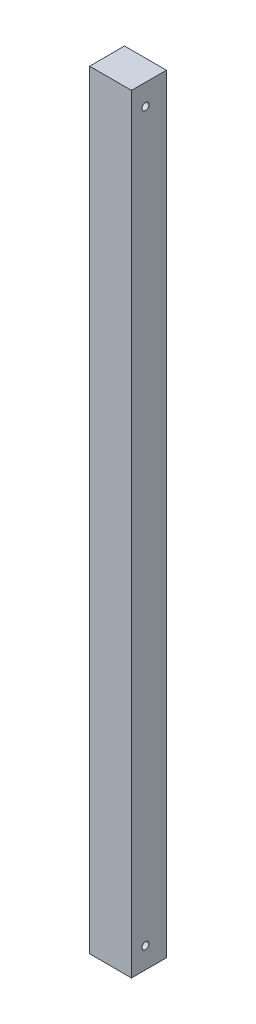
SolidWorks part; units mm, degrees
ref_plane "Front Plane" through (0, 0, 0) normal (0, 0, 1) x (1, 0, 0)
ref_plane "Top Plane" through (0, 0, 0) normal (0, 1, 0) x (1, 0, 0)
ref_plane "Right Plane" through (0, 0, 0) normal (1, 0, 0) x (0, 0, -1)
sketch "Sketch1" plane through (0, 0, 0) normal (0, 1, 0) x (1, 0, 0)
  line L0 (0, 5) -> (30, 5)
  line L2 (0, 5) -> (0, 30)
  line L3 (0, 30) -> (30, 30)
  line L4 (30, 5) -> (30, 30)
  point P5 (0, 5)
  dimension "D1" = 25
  dimension "D2" = 25
extrude "Boss-Extrude1" add sketch "Sketch1" along normal blind 550
sketch "Sketch2" plane through (30, 0, 0) normal (1, 0, 0) x (0, 0, -1)
  line L0 (5, 275) -> (30, 275) construction
  line L1 (5, 550) -> (5, 0) construction
  line L2 (30, 550) -> (30, 0) construction
  circle A0 centre (15, 15) radius 2.5
  circle A2 centre (15, 535) radius 2.5
  point P10 (0, 0)
  point P11 (0, 0)
  dimension "D1" = 5
  dimension "D2" = 520
extrude "Cut-Extrude1" cut sketch "Sketch2" against normal through all
